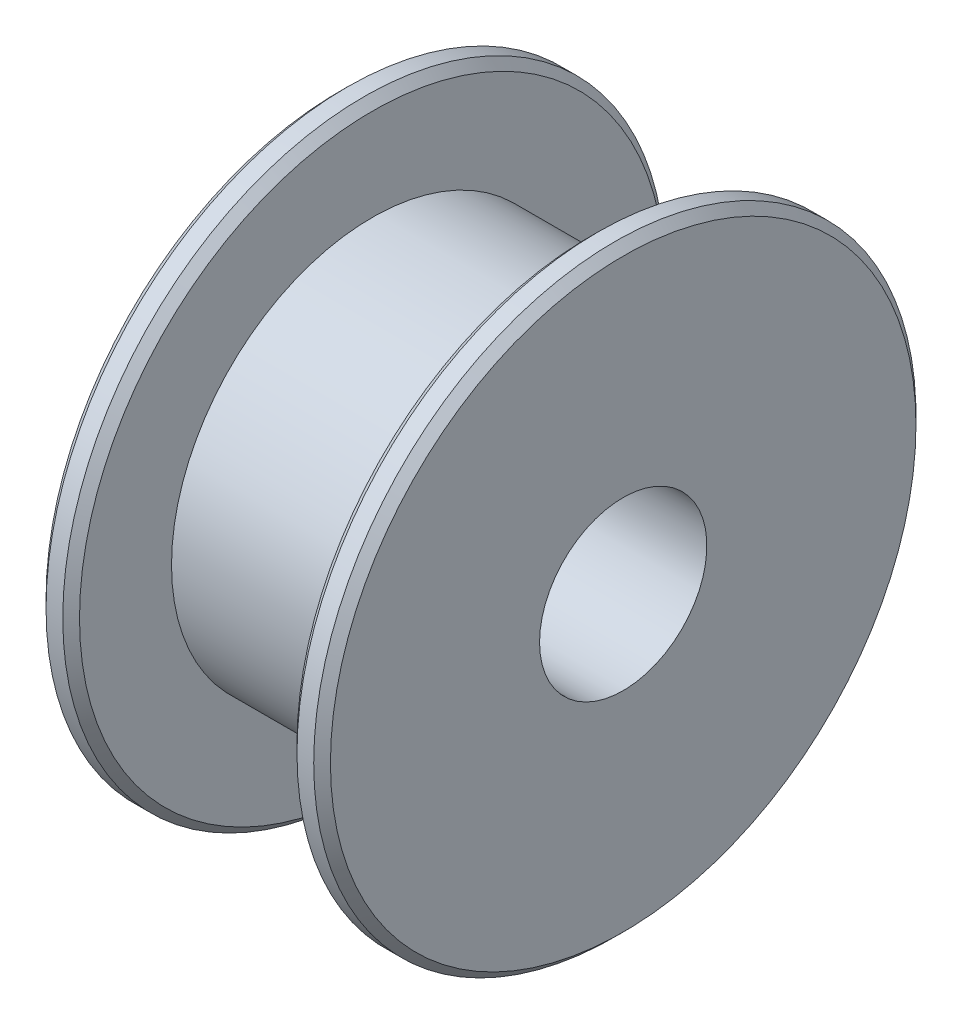
SolidWorks part; units mm, degrees
material "Lega 6061"
ref_plane "Piano frontale" through (0, 0, 0) normal (0, 0, 1) x (1, 0, 0)
ref_plane "Piano superiore" through (0, 0, 0) normal (0, 1, 0) x (1, 0, 0)
ref_plane "Piano destro" through (0, 0, 0) normal (1, 0, 0) x (0, 0, -1)
sketch "Schizzo1" plane through (0, 0, 0) normal (0, 0, 1) x (1, 0, 0)
  line L0 (0, 0) -> (13.9262, 0) construction
  line L1 (0, 2.5) -> (0, 9)
  line L2 (0, 9) -> (1, 9)
  line L3 (1, 9) -> (1, 6)
  line L4 (1, 6) -> (7.5, 6)
  line L5 (7.5, 6) -> (7.5, 9)
  line L6 (7.5, 9) -> (8.5, 9)
  line L7 (8.5, 9) -> (8.5, 2.5)
  line L9 (0, 2.5) -> (8.5, 2.5)
  dimension "D1" = 5
  dimension "D2" = 18
  dimension "D3" = 8.5
  dimension "D4" = 6.5
  dimension "D5" = 12
revolve "Rivoluzione1" add sketch "Schizzo1" angle 360 about L0
chamfer "Smusso1" distance 0.25 angle 45 4 edges at (1, 0, 9) (7.5, 0, 9) (8.5, 0, 9) (0, 0, 9)
